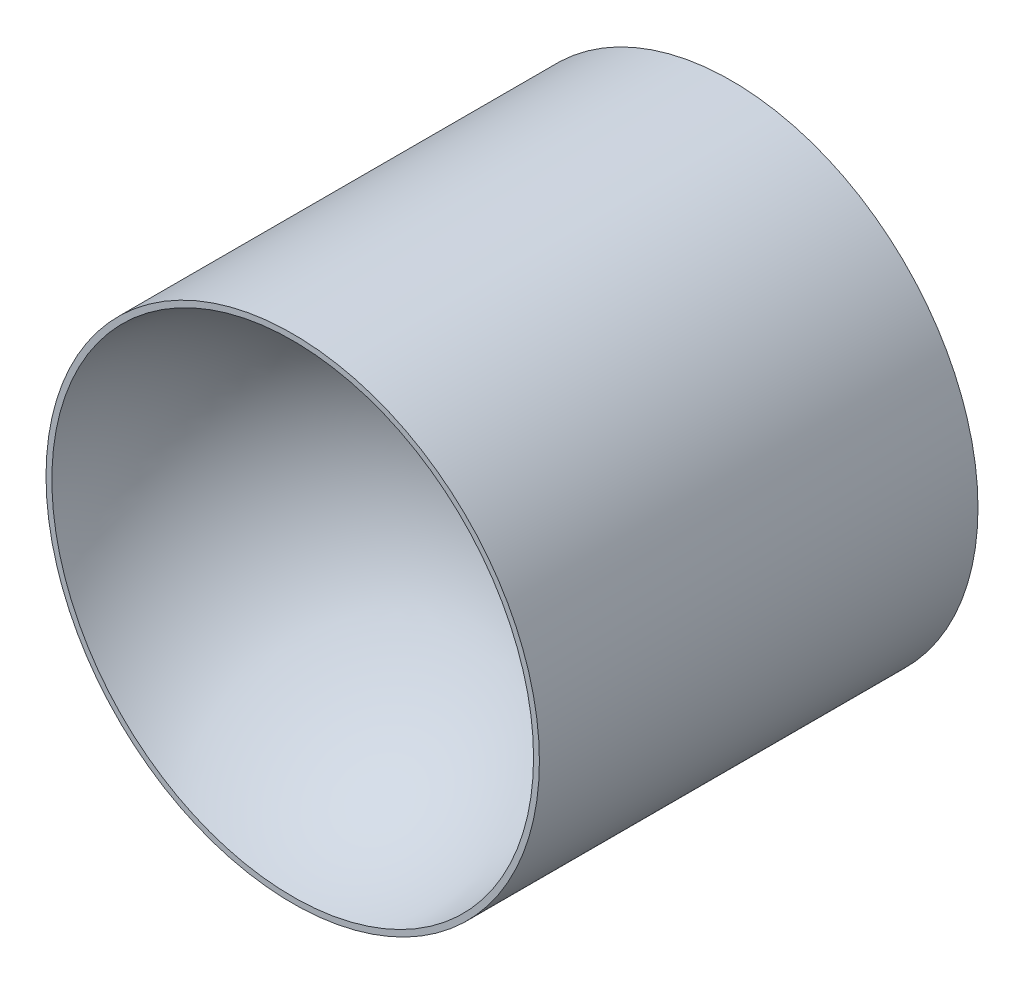
SolidWorks part; units mm, degrees
ref_plane "Front Plane" through (0, 0, 0) normal (0, 0, 1) x (1, 0, 0)
ref_plane "Top Plane" through (0, 0, 0) normal (0, 1, 0) x (1, 0, 0)
ref_plane "Right Plane" through (0, 0, 0) normal (1, 0, 0) x (0, 0, -1)
sketch "Sketch2" plane through (0, 0, 0) normal (0, 0, 1) x (1, 0, 0)
  circle A0 centre (0, 0) radius 36
  dimension "D1" = 72
extrude "Boss-Extrude1" add sketch "Sketch2" along normal blind 74
ref_plane "Plane1" through (0, 0, 69) normal (0, 0, 1) x (1, 0, 0)
sketch "Sketch4" plane through (0, 0, 69) normal (0, 0, 1) x (1, 0, 0)
  line L0 (-35.5, 0) -> (35.5, 0)
  line L1 (0, 9.3175) -> (0, -9.8919) construction
  arc A0 (-35.5, 0) -> (35.5, 0) centre (0, 0) cw
  point P6 (0, 0)
  dimension "D1" = 71
revolve "Cut-Revolve1" cut sketch "Sketch4" angle 180 about L0
ref_plane "Plane2" through (0, 0, 64) normal (0, 0, 1) x (1, 0, 0)
sketch "Sketch5" plane through (0, 0, 64) normal (0, 0, 1) x (1, 0, 0)
  line L1 (-50.4132, 43.016) -> (47.2177, 43.016)
  line L2 (-50.4132, 43.016) -> (-50.4132, -42.2852)
  line L3 (-50.4132, -42.2852) -> (47.2177, -42.2852)
  line L4 (47.2177, 43.016) -> (47.2177, -42.2852)
extrude "Cut-Extrude1" cut sketch "Sketch5" along normal up to next
sketch "Sketch6" plane through (0, 0, 0) normal (0, 0, -1) x (-1, 0, 0)
  circle A0 centre (0, 0) radius 11.5
  dimension "D1" = 23
extrude "Cut-Extrude2" cut sketch "Sketch6" against normal blind 2.5
